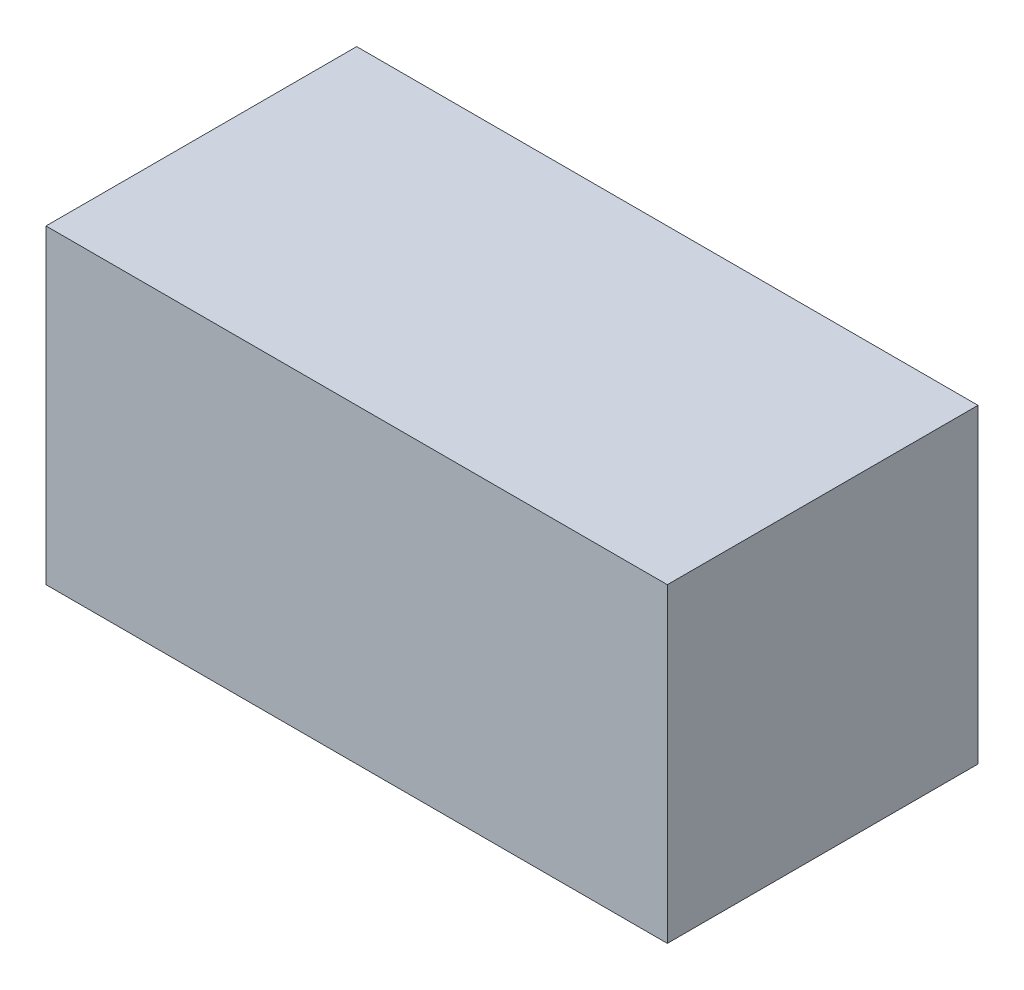
SolidWorks part; units mm, degrees
ref_plane "Front Plane" through (0, 0, 0) normal (0, 0, 1) x (1, 0, 0)
ref_plane "Top Plane" through (0, 0, 0) normal (0, 1, 0) x (1, 0, 0)
ref_plane "Right Plane" through (0, 0, 0) normal (1, 0, 0) x (0, 0, -1)
sketch "Sketch1" plane through (0, 0, 0) normal (0, 0, 1) x (1, 0, 0)
  line L1 (-50, -25) -> (50, -25)
  line L2 (-50, -25) -> (-50, 25)
  line L3 (-50, 25) -> (50, 25)
  line L4 (50, -25) -> (50, 25)
  line L5 (-50, -25) -> (50, 25) construction
  line L6 (-50, 25) -> (50, -25) construction
  point P0 (0, 0)
  dimension "D1" = 100
  dimension "D2" = 50
extrude "Boss-Extrude1" add sketch "Sketch1" along normal blind 50
